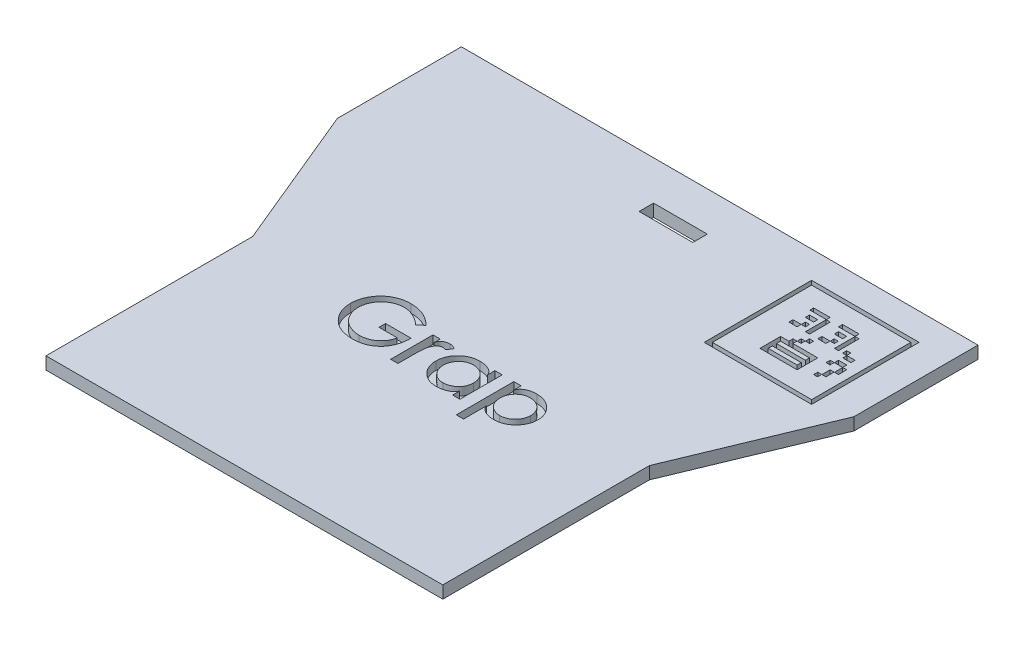
SolidWorks part; units mm, degrees
ref_plane "Alzado" through (0, 0, 0) normal (0, 0, 1) x (1, 0, 0)
ref_plane "Planta" through (0, 0, 0) normal (0, 1, 0) x (1, 0, 0)
ref_plane "Vista lateral" through (0, 0, 0) normal (1, 0, 0) x (0, 0, -1)
sketch "Croquis1" plane through (0, 0, 0) normal (0, 1, 0) x (1, 0, 0)
  line L0 (9.7917, 53.6314) -> (-115.2083, 53.6314)
  line L1 (-52.7083, 53.6314) -> (-52.7083, -61.3686) construction
  line L2 (-115.2083, 53.6314) -> (-115.2083, 23.6314) construction
  line L3 (-115.2083, 23.6314) -> (9.7917, 23.6314) construction
  line L4 (9.7917, 23.6314) -> (9.7917, 53.6314) construction
  line L5 (-115.2083, 53.6314) -> (-110.2083, 53.6314) construction
  line L6 (-110.2083, 53.6314) -> (-110.2083, 48.6314) construction
  line L7 (-100.7083, -61.3686) -> (-4.7083, -61.3686)
  line L8 (-110.2083, 48.6314) -> (-70.2083, 48.6314)
  line L9 (-110.2083, 48.6314) -> (-110.2083, 28.6314)
  line L10 (-110.2083, 28.6314) -> (-70.2083, 28.6314)
  line L11 (-70.2083, 48.6314) -> (-70.2083, 28.6314)
  line L12 (-100.7083, -61.3686) -> (-100.7083, -11.3686) construction
  line L13 (-100.7083, -61.3686) -> (-100.7083, -56.3686) construction
  line L14 (-100.7083, -56.3686) -> (-95.7083, -56.3686) construction
  line L15 (-100.7083, -61.3686) -> (-100.7083, -11.3686)
  line L16 (-95.7083, -56.3686) -> (-75.7083, -56.3686)
  line L17 (-95.7083, -56.3686) -> (-95.7083, -16.3686)
  line L18 (-95.7083, -16.3686) -> (-75.7083, -16.3686)
  line L19 (-75.7083, -56.3686) -> (-75.7083, -16.3686)
  line L20 (-100.7083, -11.3686) -> (-115.2083, 23.6314)
  line L21 (-115.2083, 23.6314) -> (-115.2083, 53.6314)
  line L22 (4.7917, 28.6314) -> (-35.2083, 28.6314)
  line L23 (4.7917, 48.6314) -> (-35.2083, 48.6314)
  line L24 (-35.2083, 48.6314) -> (-35.2083, 28.6314)
  line L25 (-29.7083, -56.3686) -> (-29.7083, -16.3686)
  line L26 (-4.7083, -56.3686) -> (-9.7083, -56.3686) construction
  line L27 (-4.7083, -61.3686) -> (-4.7083, -56.3686) construction
  line L28 (-4.7083, -61.3686) -> (-4.7083, -11.3686) construction
  line L29 (-9.7083, -16.3686) -> (-29.7083, -16.3686)
  line L30 (-9.7083, -56.3686) -> (-9.7083, -16.3686)
  line L31 (-9.7083, -56.3686) -> (-29.7083, -56.3686)
  line L32 (-4.7083, -61.3686) -> (-4.7083, -11.3686)
  line L33 (4.7917, 53.6314) -> (4.7917, 48.6314) construction
  line L34 (9.7917, 53.6314) -> (4.7917, 53.6314) construction
  line L35 (9.7917, 53.6314) -> (9.7917, 23.6314) construction
  line L36 (9.7917, 23.6314) -> (9.7917, 53.6314)
  line L37 (-4.7083, -11.3686) -> (9.7917, 23.6314)
  line L38 (4.7917, 48.6314) -> (4.7917, 28.6314)
  point P32 (-52.7083, -56.3686)
extrude "Saliente-Extruir1" add sketch "Croquis1" along normal blind 40
sketch "Croquis2" plane through (0, 0, 0) normal (0, -1, 0) x (1, 0, 0)
  line L8 (9.7917, -53.6314) -> (9.7917, -23.6314)
  line L9 (9.7917, -23.6314) -> (-4.7083, 11.3686)
  line L10 (-4.7083, 11.3686) -> (-4.7083, 61.3686)
  line L11 (-4.7083, 61.3686) -> (-100.7083, 61.3686)
  line L12 (-100.7083, 61.3686) -> (-100.7083, 11.3686)
  line L13 (-100.7083, 11.3686) -> (-115.2083, -23.6314)
  line L14 (-115.2083, -23.6314) -> (-115.2083, -53.6314)
  line L15 (-115.2083, -53.6314) -> (9.7917, -53.6314)
  line L16 (9.7917, -53.6314) -> (9.7917, -23.6314)
  line L17 (9.7917, -23.6314) -> (-4.7083, 11.3686)
  line L18 (-4.7083, 11.3686) -> (-4.7083, 61.3686)
  line L19 (-4.7083, 61.3686) -> (-100.7083, 61.3686)
  line L20 (-100.7083, 61.3686) -> (-100.7083, 11.3686)
  line L21 (-100.7083, 11.3686) -> (-115.2083, -23.6314)
  line L22 (-115.2083, -23.6314) -> (-115.2083, -53.6314)
  line L23 (-115.2083, -53.6314) -> (9.7917, -53.6314)
  dimension "D1" = 0
extrude "Saliente-Extruir2" add sketch "Croquis2" along normal blind 5
sketch "Croquis3" plane through (0, 40, 0) normal (0, 1, 0) x (1, 0, 0)
  line L0 (-52.7083, 53.6314) -> (-52.7083, -61.3686) construction
  line L1 (9.7917, 53.6314) -> (-115.2083, 53.6314) construction
  line L2 (-100.7083, -61.3686) -> (-4.7083, -61.3686) construction
  line L3 (-52.7083, 53.6314) -> (-52.7083, 44.1314) construction
  line L4 (-52.7083, 44.1314) -> (-52.7083, 40.6314) construction
  line L5 (-52.7083, 44.1314) -> (-46.2083, 44.1314) construction
  line L6 (-46.2083, 44.1314) -> (-52.7083, 40.6314) construction
  line L7 (-52.7083, 40.6314) -> (-59.2083, 40.6314) construction
  line L9 (-46.2083, 44.1314) -> (-59.2083, 44.1314)
  line L10 (-46.2083, 44.1314) -> (-46.2083, 40.6314)
  line L11 (-46.2083, 40.6314) -> (-59.2083, 40.6314)
  line L12 (-59.2083, 44.1314) -> (-59.2083, 40.6314)
extrude "Cortar-Extruir1" cut sketch "Croquis3" against normal blind 62
sketch "Croquis4" plane through (9.7917, 0, 0) normal (1, 0, 0) x (0, 0, -1)
  line L0 (53.6314, -5) -> (53.6314, -2) construction
  line L1 (53.6314, -2) -> (-83.5197, -2) construction
  line L3 (-83.5197, -2) -> (64.2232, -2)
  line L4 (-83.5197, -2) -> (-83.5197, 49.9203)
  line L5 (-83.5197, 49.9203) -> (64.2232, 49.9203)
  line L6 (64.2232, -2) -> (64.2232, 49.9203)
extrude "Cortar-Extruir2" cut sketch "Croquis4" against normal blind 152
sketch "Croquis5" plane through (0, -2, 0) normal (0, 1, 0) x (1, 0, 0)
  text T0 "<b>Grap</b>" font "Century Gothic" height in points 52
extrude "Cortar-Extruir3" cut sketch "Croquis5" against normal blind 2
sketch "Croquis6" plane through (0, -2, 0) normal (0, 1, 0) x (1, 0, 0)
  line L0 (-6.5745, 73.0713) -> (62.7588, 73.0713) construction
  line L1 (-23.9079, 47.0713) -> (2.0921, 47.0713) construction
  line L2 (2.0921, 47.0713) -> (2.0921, 21.0713) construction
  line L3 (2.0921, 21.0713) -> (-23.9079, 21.0713) construction
  line L4 (-23.9079, 21.0713) -> (-23.9079, 47.0713) construction
  line L5 (-23.9079, 47.0713) -> (-22.9079, 47.0713) construction
  line L6 (-22.9079, 47.0713) -> (-22.9079, 21.0713) construction
  line L7 (-21.9079, 47.0713) -> (-21.9079, 21.0713) construction
  line L8 (-20.9079, 47.0713) -> (-20.9079, 21.0713) construction
  line L9 (-19.9079, 47.0713) -> (-19.9079, 21.0713) construction
  line L10 (-18.9079, 47.0713) -> (-18.9079, 21.0713) construction
  line L11 (-17.9079, 47.0713) -> (-17.9079, 21.0713) construction
  line L12 (-16.9079, 47.0713) -> (-16.9079, 21.0713) construction
  line L13 (-15.9079, 47.0713) -> (-15.9079, 21.0713) construction
  line L14 (-14.9079, 47.0713) -> (-14.9079, 21.0713) construction
  line L15 (-13.9079, 47.0713) -> (-13.9079, 21.0713) construction
  line L16 (-12.9079, 47.0713) -> (-12.9079, 21.0713) construction
  line L17 (-11.9079, 47.0713) -> (-11.9079, 21.0713) construction
  line L18 (-10.9079, 47.0713) -> (-10.9079, 21.0713) construction
  line L19 (-9.9079, 47.0713) -> (-9.9079, 21.0713) construction
  line L20 (-8.9079, 47.0713) -> (-8.9079, 21.0713) construction
  line L21 (-7.9079, 47.0713) -> (-7.9079, 21.0713) construction
  line L22 (-6.9079, 47.0713) -> (-6.9079, 21.0713) construction
  line L23 (-5.9079, 47.0713) -> (-5.9079, 21.0713) construction
  line L24 (-4.9079, 47.0713) -> (-4.9079, 21.0713) construction
  line L25 (-3.9079, 47.0713) -> (-3.9079, 21.0713) construction
  line L26 (-2.9079, 47.0713) -> (-2.9079, 21.0713) construction
  line L27 (-1.9079, 47.0713) -> (-1.9079, 21.0713) construction
  line L28 (-0.9079, 47.0713) -> (-0.9079, 21.0713) construction
  line L29 (0.0921, 47.0713) -> (0.0921, 21.0713) construction
  line L30 (1.0921, 47.0713) -> (1.0921, 21.0713) construction
  line L31 (2.0921, 47.0713) -> (2.0921, 46.0713) construction
  line L32 (2.0921, 46.0713) -> (-23.9079, 46.0713) construction
  line L33 (2.0921, 45.0713) -> (-23.9079, 45.0713) construction
  line L34 (2.0921, 44.0713) -> (-23.9079, 44.0713) construction
  line L35 (2.0921, 43.0713) -> (-23.9079, 43.0713) construction
  line L36 (2.0921, 42.0713) -> (-23.9079, 42.0713) construction
  line L37 (2.0921, 41.0713) -> (-23.9079, 41.0713) construction
  line L38 (2.0921, 40.0713) -> (-23.9079, 40.0713) construction
  line L39 (2.0921, 39.0713) -> (-23.9079, 39.0713) construction
  line L40 (2.0921, 38.0713) -> (-23.9079, 38.0713) construction
  line L41 (2.0921, 37.0713) -> (-23.9079, 37.0713) construction
  line L42 (2.0921, 36.0713) -> (-23.9079, 36.0713) construction
  line L43 (2.0921, 35.0713) -> (-23.9079, 35.0713) construction
  line L44 (2.0921, 34.0713) -> (-23.9079, 34.0713) construction
  line L45 (2.0921, 33.0713) -> (-23.9079, 33.0713) construction
  line L46 (2.0921, 32.0713) -> (-23.9079, 32.0713) construction
  line L47 (2.0921, 31.0713) -> (-23.9079, 31.0713) construction
  line L48 (2.0921, 30.0713) -> (-23.9079, 30.0713) construction
  line L49 (2.0921, 29.0713) -> (-23.9079, 29.0713) construction
  line L50 (2.0921, 28.0713) -> (-23.9079, 28.0713) construction
  line L51 (2.0921, 27.0713) -> (-23.9079, 27.0713) construction
  line L52 (2.0921, 26.0713) -> (-23.9079, 26.0713) construction
  line L53 (2.0921, 25.0713) -> (-23.9079, 25.0713) construction
  line L54 (2.0921, 24.0713) -> (-23.9079, 24.0713) construction
  line L55 (2.0921, 23.0713) -> (-23.9079, 23.0713) construction
  line L56 (2.0921, 22.0713) -> (-23.9079, 22.0713) construction
  line L57 (2.0921, 44.5713) -> (-23.9079, 44.5713) construction
  line L58 (2.0921, 44.0713) -> (-23.9079, 44.0713) construction
  line L59 (2.0921, 43.5713) -> (-23.9079, 43.5713) construction
  line L60 (2.0921, 43.0713) -> (-23.9079, 43.0713) construction
  line L61 (2.0921, 42.5713) -> (-23.9079, 42.5713) construction
  line L62 (2.0921, 42.0713) -> (-23.9079, 42.0713) construction
  line L63 (2.0921, 41.5713) -> (-23.9079, 41.5713) construction
  line L64 (2.0921, 41.0713) -> (-23.9079, 41.0713) construction
  line L65 (2.0921, 40.5713) -> (-23.9079, 40.5713) construction
  line L66 (2.0921, 40.0713) -> (-23.9079, 40.0713) construction
  line L67 (2.0921, 39.5713) -> (-23.9079, 39.5713) construction
  line L68 (2.0921, 39.0713) -> (-23.9079, 39.0713) construction
  line L69 (2.0921, 38.5713) -> (-23.9079, 38.5713) construction
  line L70 (2.0921, 38.0713) -> (-23.9079, 38.0713) construction
  line L71 (2.0921, 37.5713) -> (-23.9079, 37.5713) construction
  line L72 (2.0921, 37.0713) -> (-23.9079, 37.0713) construction
  line L73 (2.0921, 36.5713) -> (-23.9079, 36.5713) construction
  line L74 (2.0921, 36.0713) -> (-23.9079, 36.0713) construction
  line L75 (2.0921, 35.5713) -> (-23.9079, 35.5713) construction
  line L76 (2.0921, 35.0713) -> (-23.9079, 35.0713) construction
  line L77 (2.0921, 34.5713) -> (-23.9079, 34.5713) construction
  line L78 (2.0921, 34.0713) -> (-23.9079, 34.0713) construction
  line L79 (2.0921, 33.5713) -> (-23.9079, 33.5713) construction
  line L80 (2.0921, 33.0713) -> (-23.9079, 33.0713) construction
  line L81 (2.0921, 32.5713) -> (-23.9079, 32.5713) construction
  line L82 (2.0921, 32.0713) -> (-23.9079, 32.0713) construction
  line L83 (2.0921, 31.5713) -> (-23.9079, 31.5713) construction
  line L84 (2.0921, 31.0713) -> (-23.9079, 31.0713) construction
  line L85 (2.0921, 30.5713) -> (-23.9079, 30.5713) construction
  line L86 (2.0921, 30.0713) -> (-23.9079, 30.0713) construction
  line L87 (2.0921, 29.5713) -> (-23.9079, 29.5713) construction
  line L88 (2.0921, 29.0713) -> (-23.9079, 29.0713) construction
  line L89 (2.0921, 28.5713) -> (-23.9079, 28.5713) construction
  line L90 (2.0921, 28.0713) -> (-23.9079, 28.0713) construction
  line L91 (2.0921, 27.5713) -> (-23.9079, 27.5713) construction
  line L92 (2.0921, 27.0713) -> (-23.9079, 27.0713) construction
  line L93 (2.0921, 26.5713) -> (-23.9079, 26.5713) construction
  line L94 (-17.9079, 41.5713) -> (-13.9079, 41.5713)
  line L95 (-13.9079, 40.5713) -> (-13.9079, 35.5713)
  line L96 (-13.9079, 40.5713) -> (-12.9079, 40.5713)
  line L97 (-12.9079, 40.5713) -> (-12.9079, 35.5713)
  line L98 (-12.9079, 35.5713) -> (-13.9079, 35.5713)
  line L99 (-12.9079, 35.5713) -> (-12.9079, 41.5713)
  line L100 (-12.9079, 41.5713) -> (-17.9079, 41.5713)
  line L101 (-17.9079, 40.5713) -> (-17.9079, 41.5713)
  line L102 (-6.9079, 41.5713) -> (-5.9079, 41.5713)
  line L103 (-16.9079, 39.5713) -> (-14.9079, 39.5713)
  line L104 (-16.9079, 39.5713) -> (-16.9079, 38.5713)
  line L105 (-16.9079, 38.5713) -> (-14.9079, 38.5713)
  line L106 (-14.9079, 39.5713) -> (-14.9079, 38.5713)
  line L107 (-15.9079, 37.5713) -> (-14.9079, 37.5713)
  line L108 (-15.9079, 37.5713) -> (-15.9079, 36.5713)
  line L109 (-15.9079, 36.5713) -> (-14.9079, 36.5713)
  line L110 (-14.9079, 37.5713) -> (-14.9079, 36.5713)
  line L111 (-17.9079, 36.5713) -> (-15.9079, 36.5713)
  line L112 (-17.9079, 36.5713) -> (-17.9079, 35.5713)
  line L113 (-17.9079, 35.5713) -> (-15.9079, 35.5713)
  line L114 (-15.9079, 36.5713) -> (-15.9079, 35.5713)
  line L115 (-10.9079, 41.5713) -> (-6.9079, 41.5713)
  line L116 (-10.9079, 41.5713) -> (-10.9079, 40.5713)
  line L117 (-10.9079, 40.5713) -> (-6.9079, 40.5713)
  line L118 (-6.9079, 41.5713) -> (-6.9079, 40.5713)
  line L119 (-6.9079, 40.5713) -> (-5.9079, 40.5713)
  line L120 (-6.9079, 40.5713) -> (-6.9079, 35.5713)
  line L121 (-6.9079, 35.5713) -> (-5.9079, 35.5713)
  line L122 (-5.9079, 40.5713) -> (-5.9079, 35.5713)
  line L123 (-9.9079, 39.5713) -> (-7.9079, 39.5713)
  line L124 (-9.9079, 39.5713) -> (-9.9079, 38.5713)
  line L125 (-9.9079, 38.5713) -> (-7.9079, 38.5713)
  line L126 (-7.9079, 39.5713) -> (-7.9079, 38.5713)
  line L127 (-8.9079, 37.5713) -> (-7.9079, 37.5713)
  line L128 (-8.9079, 37.5713) -> (-8.9079, 36.5713)
  line L129 (-8.9079, 36.5713) -> (-7.9079, 36.5713)
  line L130 (-7.9079, 37.5713) -> (-7.9079, 36.5713)
  line L131 (-10.9079, 36.5713) -> (-8.9079, 36.5713)
  line L132 (-10.9079, 36.5713) -> (-10.9079, 35.5713)
  line L133 (-10.9079, 35.5713) -> (-8.9079, 35.5713)
  line L134 (-8.9079, 36.5713) -> (-8.9079, 35.5713)
  line L135 (-4.9079, 36.5713) -> (-3.9079, 36.5713)
  line L136 (-4.9079, 36.5713) -> (-4.9079, 35.5713)
  line L137 (-4.9079, 35.5713) -> (-3.9079, 35.5713)
  line L138 (-3.9079, 36.5713) -> (-3.9079, 35.5713)
  line L139 (-3.9079, 35.5713) -> (-1.9079, 35.5713)
  line L140 (-3.9079, 35.5713) -> (-3.9079, 34.5713)
  line L141 (-3.9079, 34.5713) -> (-1.9079, 34.5713)
  line L142 (-1.9079, 35.5713) -> (-1.9079, 34.5713)
  line L143 (-3.9079, 33.5713) -> (-1.9079, 33.5713)
  line L144 (-3.9079, 33.5713) -> (-3.9079, 32.5713)
  line L145 (-3.9079, 32.5713) -> (-1.9079, 32.5713)
  line L146 (-1.9079, 33.5713) -> (-1.9079, 32.5713)
  line L147 (-1.9079, 32.5713) -> (-0.9079, 32.5713)
  line L148 (-1.9079, 32.5713) -> (-1.9079, 30.5713)
  line L149 (-1.9079, 30.5713) -> (-0.9079, 30.5713)
  line L150 (-0.9079, 32.5713) -> (-0.9079, 30.5713)
  line L151 (-2.9079, 30.5713) -> (-1.9079, 30.5713)
  line L152 (-2.9079, 30.5713) -> (-2.9079, 28.5713)
  line L153 (-2.9079, 28.5713) -> (-1.9079, 28.5713)
  line L154 (-1.9079, 30.5713) -> (-1.9079, 28.5713)
  line L155 (-3.9079, 28.5713) -> (-2.9079, 28.5713)
  line L156 (-3.9079, 28.5713) -> (-3.9079, 27.5713)
  line L157 (-3.9079, 27.5713) -> (-2.9079, 27.5713)
  line L158 (-2.9079, 28.5713) -> (-2.9079, 27.5713)
  line L159 (-4.9079, 32.5713) -> (-3.9079, 32.5713)
  line L160 (-4.9079, 32.5713) -> (-4.9079, 31.5713)
  line L161 (-4.9079, 31.5713) -> (-3.9079, 31.5713)
  line L162 (-3.9079, 32.5713) -> (-3.9079, 31.5713)
  line L163 (-11.9079, 34.5713) -> (-10.9079, 34.5713)
  line L164 (-11.9079, 34.5713) -> (-11.9079, 33.5713)
  line L165 (-11.9079, 33.5713) -> (-10.9079, 33.5713)
  line L166 (-10.9079, 34.5713) -> (-10.9079, 33.5713)
  line L167 (-12.9079, 33.5713) -> (-11.9079, 33.5713)
  line L168 (-12.9079, 33.5713) -> (-12.9079, 32.5713)
  line L169 (-12.9079, 32.5713) -> (-11.9079, 32.5713)
  line L170 (-11.9079, 33.5713) -> (-11.9079, 32.5713)
  line L171 (-13.9079, 32.5713) -> (-12.9079, 32.5713)
  line L172 (-13.9079, 32.5713) -> (-13.9079, 31.5713)
  line L173 (-13.9079, 31.5713) -> (-12.9079, 31.5713)
  line L174 (-12.9079, 32.5713) -> (-12.9079, 31.5713)
  line L175 (-15.9079, 31.5713) -> (-6.9079, 31.5713)
  line L176 (-15.9079, 31.5713) -> (-15.9079, 26.5713)
  line L177 (-15.9079, 26.5713) -> (-6.9079, 26.5713)
  line L178 (-6.9079, 31.5713) -> (-6.9079, 26.5713)
  line L179 (-14.9079, 30.5713) -> (-7.9079, 30.5713)
  line L180 (-14.9079, 30.5713) -> (-14.9079, 29.5713)
  line L181 (-14.9079, 29.5713) -> (-7.9079, 29.5713)
  line L182 (-7.9079, 30.5713) -> (-7.9079, 29.5713)
  line L183 (-14.9079, 28.5713) -> (-7.9079, 28.5713)
  line L184 (-14.9079, 28.5713) -> (-14.9079, 27.5713)
  line L185 (-14.9079, 27.5713) -> (-7.9079, 27.5713)
  line L186 (-7.9079, 28.5713) -> (-7.9079, 27.5713)
  line L187 (-22.9079, 46.0713) -> (1.0921, 46.0713)
  line L188 (-22.9079, 46.0713) -> (-22.9079, 22.0713)
  line L189 (-22.9079, 22.0713) -> (1.0921, 22.0713)
  line L190 (1.0921, 46.0713) -> (1.0921, 22.0713)
  line L191 (2.0921, 21.0713) -> (-23.9079, 21.0713)
  line L192 (2.0921, 21.0713) -> (2.0921, 47.0713)
  line L193 (2.0921, 47.0713) -> (-23.9079, 47.0713)
  line L194 (-23.9079, 21.0713) -> (-23.9079, 47.0713)
  line L195 (-5.9079, 41.5713) -> (-5.9079, 40.5713)
  line L196 (-1.9079, 32.6807) -> (-1.7838, 32.6807)
  line L197 (-1.7838, 32.6807) -> (-1.7838, 32.5713)
  line L198 (-1.7838, 32.5713) -> (-1.9079, 32.5713)
  line L199 (-3.9079, 32.5713) -> (-3.9079, 32.6807)
  line L200 (-3.9079, 32.6807) -> (-4.0486, 32.6807)
  line L201 (-4.0486, 32.6807) -> (-4.0486, 32.5713)
  line L202 (-4.0486, 32.5713) -> (-3.9079, 32.5713)
  line L203 (-1.9079, 30.7635) -> (-2.168, 30.7635)
  line L204 (-2.168, 30.7635) -> (-2.168, 30.5713)
  line L205 (-2.168, 30.5713) -> (-1.9079, 30.5713)
  line L206 (-2.9079, 28.5713) -> (-2.9079, 28.7479)
  line L207 (-2.9079, 28.7479) -> (-3.1789, 28.7479)
  line L208 (-3.1789, 28.7479) -> (-3.1789, 28.5713)
  line L209 (-3.1789, 28.5713) -> (-2.9079, 28.5713)
  line L210 (-13.0438, 32.6107) -> (-12.9079, 32.6107)
  line L211 (-12.9079, 32.6107) -> (-12.9079, 32.5713)
  line L212 (-13.0438, 32.5713) -> (-13.0438, 32.6107)
  line L213 (-11.9079, 33.5713) -> (-11.9079, 33.5931)
  line L214 (-11.9079, 33.5931) -> (-11.9598, 33.5931)
  line L215 (-11.9598, 33.5931) -> (-11.9598, 33.5713)
  line L216 (-11.9598, 33.5713) -> (-11.9079, 33.5713)
  line L217 (-8.9079, 36.5713) -> (-8.9079, 36.6899)
  line L218 (-8.9079, 36.6899) -> (-9.22, 36.6899)
  line L219 (-9.22, 36.6899) -> (-9.22, 36.5713)
  line L220 (-9.22, 36.5713) -> (-8.9079, 36.5713)
  line L221 (-8.9079, 36.5713) -> (-8.9079, 36.6899)
  line L222 (-15.9079, 36.5713) -> (-15.9079, 36.6899)
  line L223 (-15.9079, 36.6899) -> (-16.1662, 36.6899)
  line L224 (-16.1662, 36.6899) -> (-16.1662, 36.5713)
  line L225 (-16.1662, 36.5713) -> (-15.9079, 36.5713)
  dimension "D1" = 25
  dimension "D2" = 25
  dimension "D3" = 38
extrude "Cortar-Extruir7" cut sketch "Croquis6" against normal blind 2 contours L194 L191 L192 L193 L187 L190 L189 L188
sketch "Croquis7" plane through (0, -2, 0) normal (0, 1, 0) x (1, 0, 0)
  line L1 (-17.8863, 41.5281) -> (-13.8953, 41.5281)
  line L2 (-17.8863, 41.5281) -> (-17.8863, 40.6302)
  line L3 (-17.8863, 40.6302) -> (-13.8953, 40.6302)
  line L4 (-13.8953, 41.5281) -> (-13.8953, 40.6302)
  line L5 (-16.8886, 39.5576) -> (-14.918, 39.5576)
  line L6 (-16.8886, 39.5576) -> (-16.8886, 38.5599)
  line L7 (-16.8886, 38.5599) -> (-14.918, 38.5599)
  line L8 (-14.918, 39.5576) -> (-14.918, 38.5599)
  point P0 (-16.8886, 39.5576)
  point P1 (-14.918, 38.5599)
  point P2 (-17.8863, 41.5281)
  point P3 (-13.8953, 40.6302)
extrude "Cortar-Extruir8" cut sketch "Croquis7" against normal blind 2
sketch "Croquis8" plane through (0, -2, 0) normal (0, 1, 0) x (1, 0, 0)
  line L1 (-13.8905, 40.5729) -> (-12.8976, 40.5729)
  line L2 (-13.8905, 40.5729) -> (-13.8905, 35.5417)
  line L3 (-13.8905, 35.5417) -> (-12.8976, 35.5417)
  line L4 (-12.8976, 40.5729) -> (-12.8976, 35.5417)
  point P0 (-12.8976, 35.5417)
extrude "Cortar-Extruir10" cut sketch "Croquis8" against normal blind 2
sketch "Croquis9" plane through (0, -2, 0) normal (0, 1, 0) x (1, 0, 0)
  line L0 (-17.9079, 35.5713) -> (-15.9079, 35.5713) construction
  line L1 (-15.9133, 37.5751) -> (-14.9079, 37.5751)
  line L2 (-15.9133, 37.5751) -> (-15.9133, 36.5713)
  line L3 (-15.9133, 36.5713) -> (-14.9079, 36.5713)
  line L4 (-14.9079, 37.5751) -> (-14.9079, 36.5713)
  line L5 (-17.9079, 36.5713) -> (-15.9346, 36.5713)
  line L6 (-17.9079, 36.5713) -> (-17.9079, 35.5713)
  line L7 (-17.9079, 35.5713) -> (-15.9346, 35.5713)
  line L8 (-15.9346, 36.5713) -> (-15.9346, 35.5713)
  line L9 (2.0921, 41.5713) -> (-23.9079, 41.5713) construction
  line L10 (-10.9079, 41.5713) -> (-6.9079, 41.5713)
  line L11 (-10.9079, 41.5713) -> (-10.9079, 40.5713)
  line L12 (-10.9079, 40.5713) -> (-6.9079, 40.5713)
  line L13 (-6.9079, 41.5713) -> (-6.9079, 40.5713)
  line L14 (-6.9079, 40.5713) -> (-5.9079, 40.5713) construction
  line L15 (-6.8727, 40.5713) -> (-5.9079, 40.5713)
  line L16 (-6.8727, 40.5713) -> (-6.8727, 35.5713)
  line L17 (-6.8727, 35.5713) -> (-5.9079, 35.5713)
  line L18 (-5.9079, 40.5713) -> (-5.9079, 35.5713)
  line L19 (-8.9079, 37.5713) -> (-8.9079, 36.5713) construction
  line L20 (-9.9079, 39.5713) -> (-7.9079, 39.5713)
  line L21 (-9.9079, 39.5713) -> (-9.9079, 38.5713)
  line L22 (-9.9079, 38.5713) -> (-7.9079, 38.5713)
  line L23 (-7.9079, 39.5713) -> (-7.9079, 38.5713)
  line L24 (-4.9079, 36.5713) -> (-3.9079, 36.5713)
  line L25 (-4.9079, 36.5713) -> (-4.9079, 35.5713)
  line L26 (-4.9079, 35.5713) -> (-3.9079, 35.5713)
  line L27 (-3.9079, 36.5713) -> (-3.9079, 35.5713)
  line L28 (-8.9079, 37.5237) -> (-7.9079, 37.5237)
  line L29 (-8.9079, 37.5237) -> (-8.9079, 36.5713)
  line L30 (-8.9079, 36.5713) -> (-7.9079, 36.5713)
  line L31 (-7.9079, 37.5237) -> (-7.9079, 36.5713)
  line L32 (-10.9079, 35.5713) -> (-8.9079, 35.5713) construction
  line L33 (-10.9079, 36.5713) -> (-8.9501, 36.5713)
  line L34 (-10.9079, 36.5713) -> (-10.9079, 35.5713)
  line L35 (-10.9079, 35.5713) -> (-8.9501, 35.5713)
  line L36 (-8.9501, 36.5713) -> (-8.9501, 35.5713)
  line L37 (-3.9079, 35.5713) -> (-1.9079, 35.5713) construction
  line L38 (-3.8781, 35.5713) -> (-1.9079, 35.5713)
  line L39 (-3.8781, 35.5713) -> (-3.8781, 34.5713)
  line L40 (-3.8781, 34.5713) -> (-1.9079, 34.5713)
  line L41 (-1.9079, 35.5713) -> (-1.9079, 34.5713)
  line L42 (-4.9079, 31.5713) -> (-3.9079, 31.5713) construction
  line L43 (-3.9079, 33.5713) -> (-1.9079, 33.5713)
  line L44 (-3.9079, 33.5713) -> (-3.9079, 32.5713)
  line L45 (-3.9079, 32.5713) -> (-1.9079, 32.5713)
  line L46 (-1.9079, 33.5713) -> (-1.9079, 32.5713)
  line L47 (-4.9079, 32.5713) -> (-3.9511, 32.5713)
  line L48 (-4.9079, 32.5713) -> (-4.9079, 31.5713)
  line L49 (-4.9079, 31.5713) -> (-3.9511, 31.5713)
  line L50 (-3.9511, 32.5713) -> (-3.9511, 31.5713)
  line L51 (-1.9079, 32.5713) -> (-0.9079, 32.5713) construction
  line L52 (-1.8741, 32.5713) -> (-0.9079, 32.5713)
  line L53 (-1.8741, 32.5713) -> (-1.8741, 30.5713)
  line L54 (-1.8741, 30.5713) -> (-0.9079, 30.5713)
  line L55 (-0.9079, 32.5713) -> (-0.9079, 30.5713)
  line L56 (-2.9079, 28.5713) -> (-1.9079, 28.5713) construction
  line L57 (-2.9079, 30.5713) -> (-1.9441, 30.5713)
  line L58 (-2.9079, 30.5713) -> (-2.9079, 28.5713)
  line L59 (-2.9079, 28.5713) -> (-1.9441, 28.5713)
  line L60 (-1.9441, 30.5713) -> (-1.9441, 28.5713)
  line L61 (-3.9079, 27.5713) -> (-2.9079, 27.5713) construction
  line L62 (-3.9079, 28.5713) -> (-2.9615, 28.5713)
  line L63 (-3.9079, 28.5713) -> (-3.9079, 27.5713)
  line L64 (-3.9079, 27.5713) -> (-2.9615, 27.5713)
  line L65 (-2.9615, 28.5713) -> (-2.9615, 27.5713)
  line L66 (-12.9079, 32.5713) -> (-11.9079, 32.5713) construction
  line L67 (-11.9079, 34.5713) -> (-10.9079, 34.5713)
  line L68 (-11.9079, 34.5713) -> (-11.9079, 33.5713)
  line L69 (-11.9079, 33.5713) -> (-10.9079, 33.5713)
  line L70 (-10.9079, 34.5713) -> (-10.9079, 33.5713)
  line L71 (-12.9079, 33.5713) -> (-11.9586, 33.5713)
  line L72 (-12.9079, 33.5713) -> (-12.9079, 32.5713)
  line L73 (-12.9079, 32.5713) -> (-11.9586, 32.5713)
  line L74 (-11.9586, 33.5713) -> (-11.9586, 32.5713)
  line L76 (-13.9079, 32.5713) -> (-12.929, 32.5713)
  line L77 (-13.9079, 32.5713) -> (-13.9079, 31.1824)
  line L78 (-13.9079, 31.1824) -> (-12.929, 31.1824)
  line L79 (-12.929, 32.5713) -> (-12.929, 31.1824)
  point P0 (-15.9133, 37.5751)
extrude "Cortar-Extruir11" cut sketch "Croquis9" against normal blind 2
sketch "Croquis10" plane through (0, -2, 0) normal (0, 1, 0) x (1, 0, 0)
  line L1 (-15.9079, 31.5713) -> (-6.9079, 31.5713)
  line L2 (-15.9079, 31.5713) -> (-15.9079, 26.5713)
  line L3 (-15.9079, 26.5713) -> (-6.9079, 26.5713)
  line L4 (-6.9079, 31.5713) -> (-6.9079, 26.5713)
  line L5 (-14.9079, 30.5713) -> (-7.9079, 30.5713)
  line L6 (-14.9079, 30.5713) -> (-14.9079, 29.5713)
  line L7 (-14.9079, 29.5713) -> (-7.9079, 29.5713)
  line L8 (-7.9079, 30.5713) -> (-7.9079, 29.5713)
  line L9 (-14.9079, 28.5713) -> (-7.9079, 28.5713)
  line L10 (-14.9079, 28.5713) -> (-14.9079, 27.5713)
  line L11 (-14.9079, 27.5713) -> (-7.9079, 27.5713)
  line L12 (-7.9079, 28.5713) -> (-7.9079, 27.5713)
extrude "Cortar-Extruir12" cut sketch "Croquis10" against normal blind 2
